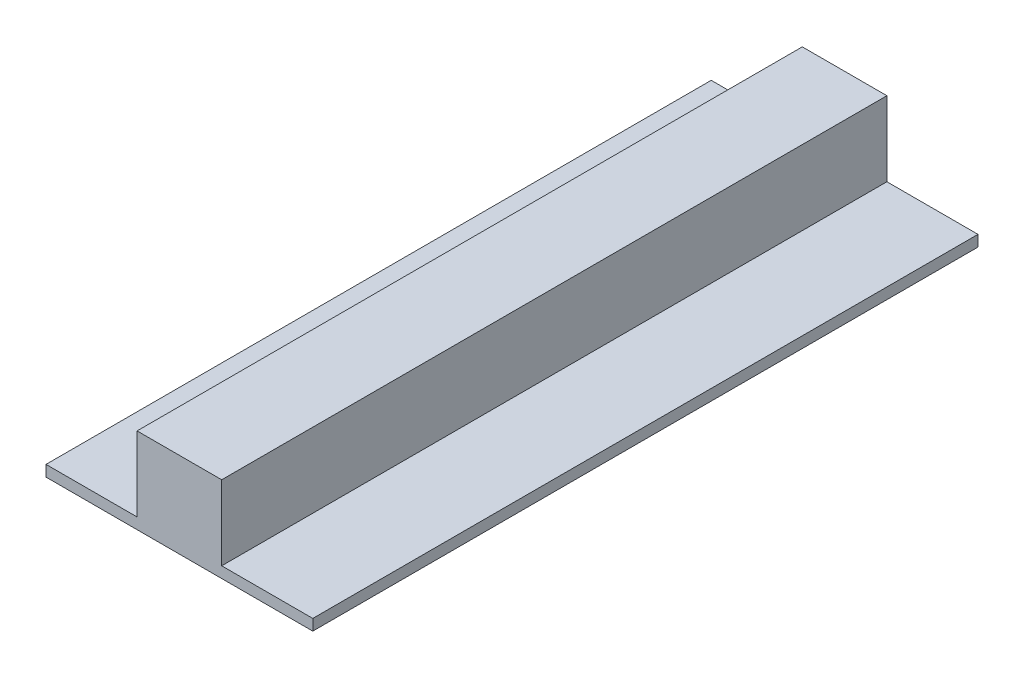
SolidWorks part; units mm, degrees
ref_plane "Front Plane" through (0, 0, 0) normal (0, 0, 1) x (1, 0, 0)
ref_plane "Top Plane" through (0, 0, 0) normal (0, 1, 0) x (1, 0, 0)
ref_plane "Right Plane" through (0, 0, 0) normal (1, 0, 0) x (0, 0, -1)
sketch "Sketch1" plane through (0, 0, 0) normal (0, 0, 1) x (1, 0, 0)
  line L0 (40.8284, -15.5) -> (48.3284, -15.5)
  line L1 (48.3284, -15.5) -> (48.3284, -11.5)
  line L2 (48.3284, -11.5) -> (40.8284, -11.5)
  line L3 (-48.3284, -15.5) -> (-40.8284, -15.5)
  line L4 (-40.8284, -11.5) -> (-48.3284, -11.5)
  line L5 (-48.3284, -11.5) -> (-48.3284, -15.5)
  line L6 (-40.8284, -15.5) -> (40.8284, -15.5)
  line L7 (40.8284, -11.5) -> (15.3284, -11.5)
  line L8 (15.3284, -11.5) -> (15.3284, 15.5)
  line L9 (15.3284, 15.5) -> (-15.3284, 15.5)
  line L10 (-15.3284, 15.5) -> (-15.3284, -11.5)
  line L11 (-15.3284, -11.5) -> (-40.8284, -11.5)
extrude "Boss-Extrude1" add sketch "Sketch1" along normal blind 241
